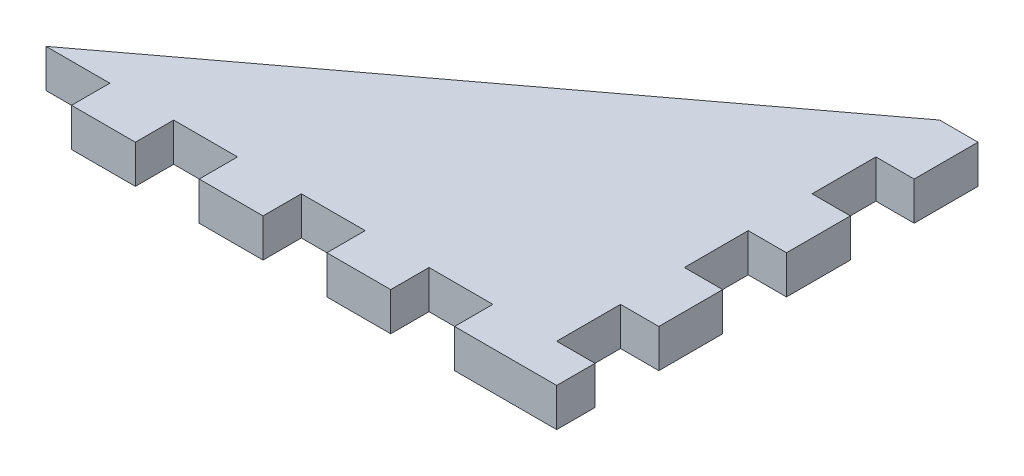
SolidWorks part; units mm, degrees
ref_plane "Front Plane" through (0, 0, 0) normal (0, 0, 1) x (1, 0, 0)
ref_plane "Top Plane" through (0, 0, 0) normal (0, 1, 0) x (1, 0, 0)
ref_plane "Right Plane" through (0, 0, 0) normal (1, 0, 0) x (0, 0, -1)
sketch "Sketch1" plane through (0, 0, 0) normal (0, 1, 0) x (1, 0, 0)
  line L0 (20, 15) -> (-20, -15)
  line L1 (-20, 15) -> (20, 15)
  line L2 (-20, 15) -> (-20, -15)
  line L3 (-20, -15) -> (20, -15)
  line L4 (20, 15) -> (20, -15)
  line L5 (-20, 15) -> (20, -15) construction
  line L6 (-20, -15) -> (20, 15) construction
  point P0 (0, 0)
  dimension "D1" = 40
  dimension "D2" = 30
extrude "Boss-Extrude1" add sketch "Sketch1" along normal mid plane 3 contours L4 L0 L3
sketch "Sketch2" plane through (20, 0, 0) normal (1, 0, 0) x (0, 0, -1)
  line L5 (15, -1.5) -> (-15, -1.5) construction
  line L14 (15, 1.5) -> (10, 1.5)
  line L15 (15, 1.5) -> (15, -1.5)
  line L16 (15, -1.5) -> (10, -1.5)
  line L17 (10, 1.5) -> (10, -1.5)
  line L19 (10, 1.5) -> (5, 1.5)
  line L20 (10, 1.5) -> (10, -1.5)
  line L21 (10, -1.5) -> (5, -1.5)
  line L22 (5, 1.5) -> (5, -1.5)
  line L23 (5, 1.5) -> (0, 1.5)
  line L24 (5, 1.5) -> (5, -1.5)
  line L25 (5, -1.5) -> (0, -1.5)
  line L26 (0, 1.5) -> (0, -1.5)
  line L27 (0, 1.5) -> (-5, 1.5)
  line L28 (0, 1.5) -> (0, -1.5)
  line L29 (0, -1.5) -> (-5, -1.5)
  line L30 (-5, 1.5) -> (-5, -1.5)
  line L31 (-5, 1.5) -> (-10, 1.5)
  line L32 (-5, 1.5) -> (-5, -1.5)
  line L33 (-5, -1.5) -> (-10, -1.5)
  line L34 (-10, 1.5) -> (-10, -1.5)
  line L35 (-10, 1.5) -> (-15, 1.5)
  line L36 (-10, 1.5) -> (-10, -1.5)
  line L37 (-10, -1.5) -> (-15, -1.5)
  line L38 (-15, 1.5) -> (-15, -1.5)
  line M7 (-15, -1.5) -> (15, -1.5)
  line M8 (15, -1.5) -> (15, 1.5)
  line M9 (15, 1.5) -> (-15, 1.5)
  dimension "D1" = 5
extrude "Boss-Extrude2" add sketch "Sketch2" along normal blind 3 contours L17 M9 M7 M8 | L26 L22 M9 M7 | L34 L30 M9 M7
sketch "Sketch3" plane through (0, 0, 15) normal (0, 0, 1) x (1, 0, 0)
  line L0 (-20, 1.5) -> (20, 1.5) construction
  line L1 (20, -1.5) -> (15, -1.5)
  line L2 (20, -1.5) -> (20, 1.5)
  line L3 (20, 1.5) -> (15, 1.5)
  line L4 (15, -1.5) -> (15, 1.5)
  line L5 (-20, -1.5) -> (20, -1.5) construction
  line L6 (15, 1.5) -> (10, 1.5)
  line L7 (15, 1.5) -> (15, -1.5)
  line L8 (15, -1.5) -> (10, -1.5)
  line L9 (10, 1.5) -> (10, -1.5)
  line L11 (10, 1.5) -> (5, 1.5)
  line L12 (10, 1.5) -> (10, -1.5)
  line L13 (10, -1.5) -> (5, -1.5)
  line L14 (5, 1.5) -> (5, -1.5)
  line L15 (5, 1.5) -> (0, 1.5)
  line L16 (5, 1.5) -> (5, -1.5)
  line L17 (5, -1.5) -> (0, -1.5)
  line L18 (0, 1.5) -> (0, -1.5)
  line L19 (0, 1.5) -> (-5, 1.5)
  line L20 (0, 1.5) -> (0, -1.5)
  line L21 (0, -1.5) -> (-5, -1.5)
  line L22 (-5, 1.5) -> (-5, -1.5)
  line L23 (-5, 1.5) -> (-10, 1.5)
  line L24 (-5, 1.5) -> (-5, -1.5)
  line L25 (-5, -1.5) -> (-10, -1.5)
  line L26 (-10, 1.5) -> (-10, -1.5)
  line L27 (-10, 1.5) -> (-15, 1.5)
  line L28 (-10, 1.5) -> (-10, -1.5)
  line L29 (-10, -1.5) -> (-15, -1.5)
  line L30 (-15, 1.5) -> (-15, -1.5)
  line L31 (-15, 1.5) -> (-20, 1.5)
  line L32 (-15, 1.5) -> (-15, -1.5)
  line L33 (-15, -1.5) -> (-20, -1.5)
  line L34 (-20, 1.5) -> (-20, -1.5)
  point P23 (0, 0)
  line M21 (-20, -1.5) -> (20, -1.5)
  line M22 (20, -1.5) -> (20, 1.5)
  line M23 (20, 1.5) -> (-20, 1.5)
  dimension "D1" = 5
extrude "Boss-Extrude3" add sketch "Sketch3" along normal blind 3 contours L4 M21 M22 M23 | L14 L9 M23 M21 | L22 L18 M23 M21 | L30 L26 M23 M21
sketch "Sketch4" plane through (20, 0, 0) normal (1, 0, 0) x (0, 0, -1)
  line L1 (-18, -1.5) -> (-15, -1.5)
  line L2 (-18, -1.5) -> (-18, 1.5)
  line L3 (-18, 1.5) -> (-15, 1.5)
  line L4 (-15, -1.5) -> (-15, 1.5)
  point P7 (0, 0)
  dimension "D1" = 3
extrude "Boss-Extrude4" add sketch "Sketch4" along normal blind 3
